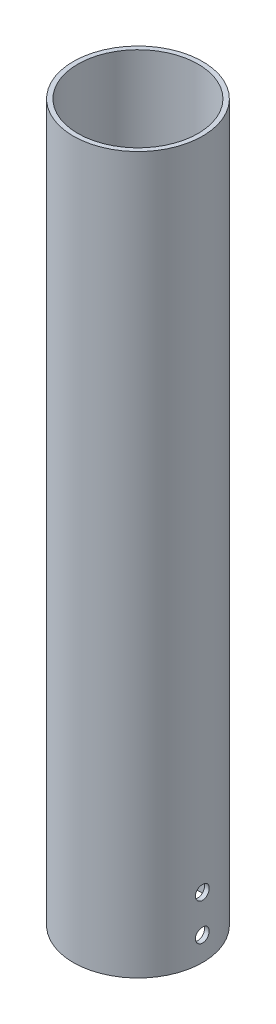
SolidWorks part; units mm, degrees
ref_plane "Front Plane" through (0, 0, 0) normal (0, 0, 1) x (1, 0, 0)
ref_plane "Top Plane" through (0, 0, 0) normal (0, 1, 0) x (1, 0, 0)
ref_plane "Right Plane" through (0, 0, 0) normal (1, 0, 0) x (0, 0, -1)
sketch "Sketch1" plane through (0, 0, 0) normal (0, 1, 0) x (1, 0, 0)
  circle A0 centre (0, 0) radius 27.1
  circle A1 centre (0, 0) radius 25.2
  dimension "D1" = 54.2
  dimension "D2" = 50.4
extrude "Boss-Extrude1" add sketch "Sketch1" along normal blind 300
sketch "Sketch2" plane through (0, 0, 0) normal (1, 0, 0) x (0, 0, -1)
  line L0 (0, 0) -> (0, 10)
  line L1 (0, 10) -> (0, 25.5)
  circle A0 centre (0, 10) radius 2.9
  circle A1 centre (0, 25.5) radius 2.9
  dimension "D1" = 5.8
  dimension "D2" = 5.8
  dimension "D3" = 10
  dimension "D4" = 15.5
extrude "Cut-Extrude1" cut sketch "Sketch2" against normal through all both and the other way through all
equation "\"TubeOutsideDiameter\"= 52"
equation "\"D1@Sketch1\"=\"CardTubeOutsideDiameter\""
equation "\"TubeInnerDiameter\"= 47.8"
equation "\"ReleaseMechanisumHeight\"=100"
equation "\"WireDiameter\"=3.38983"
equation "\"servoHoleDiameter\" = 2.8"
equation "\"CordDiameter\"= 5"
equation "\"MountingBoldDiameter\"=2.8"
equation "\"TubeMountingBoltDiameter\" = 5"
equation "\"D2@Sketch1\"=\"CardTubeInsideDiameter\""
equation "\"CardTubeOutsideDiameter\"= 54.2"
equation "\"CardTubeInsideDiameter\"= 50.4"
equation "\"D1@Sketch2\"=\"TubeMountingBoltDiameter\"+0.8"
equation "\"D2@Sketch2\"=\"TubeMountingBoltDiameter\"+0.8"
